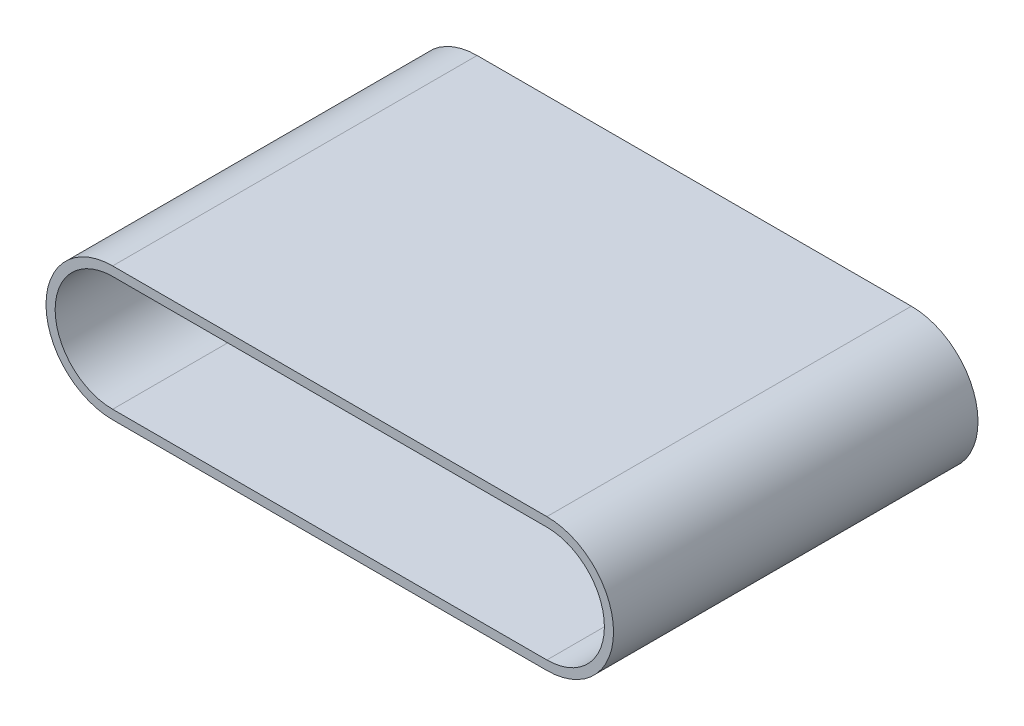
SolidWorks part; units mm, degrees
ref_plane "Front Plane" through (0, 0, 0) normal (0, 0, 1) x (1, 0, 0)
ref_plane "Top Plane" through (0, 0, 0) normal (0, 1, 0) x (1, 0, 0)
ref_plane "Right Plane" through (0, 0, 0) normal (1, 0, 0) x (0, 0, -1)
sketch "Sketch1" plane through (0, 0, 0) normal (0, 0, 1) x (1, 0, 0)
  line L0 (0, 0) -> (8.34, 0) construction
  line L1 (0, 1.28) -> (8.34, 1.28)
  line L2 (0, -1.28) -> (8.34, -1.28)
  line L3 (0, 0) -> (8.34, 0) construction
  line L4 (0, 1.1045) -> (8.34, 1.1045)
  line L5 (0, -1.1045) -> (8.34, -1.1045)
  arc A0 (0, 1.28) -> (0, -1.28) centre (0, 0) ccw
  arc A1 (8.34, -1.28) -> (8.34, 1.28) centre (8.34, 0) ccw
  arc A2 (0, 1.1045) -> (0, -1.1045) centre (0, 0) ccw
  arc A3 (8.34, -1.1045) -> (8.34, 1.1045) centre (8.34, 0) ccw
  point P3 (4.17, 0)
  point P10 (4.17, 0)
extrude "Boss-Extrude1" add sketch "Sketch1" along normal blind 7
sketch "Sketch2" plane through (0, 0, 0) normal (0, 0, -1) x (-1, 0, 0)
  line L0 (0, 0) -> (-8.3502, 0) construction
  line L1 (0, -0.1599) -> (-8.3502, -0.1599)
  line L2 (0, 0.1599) -> (-8.3502, 0.1599)
  arc A0 (0, -0.1599) -> (0, 0.1599) centre (0, 0) ccw
  arc A1 (-8.3502, 0.1599) -> (-8.3502, -0.1599) centre (-8.3502, 0) ccw
  point P3 (-4.1751, 0)
extrude "Boss-Extrude3" add sketch "Sketch2" against normal blind 5 separate body
